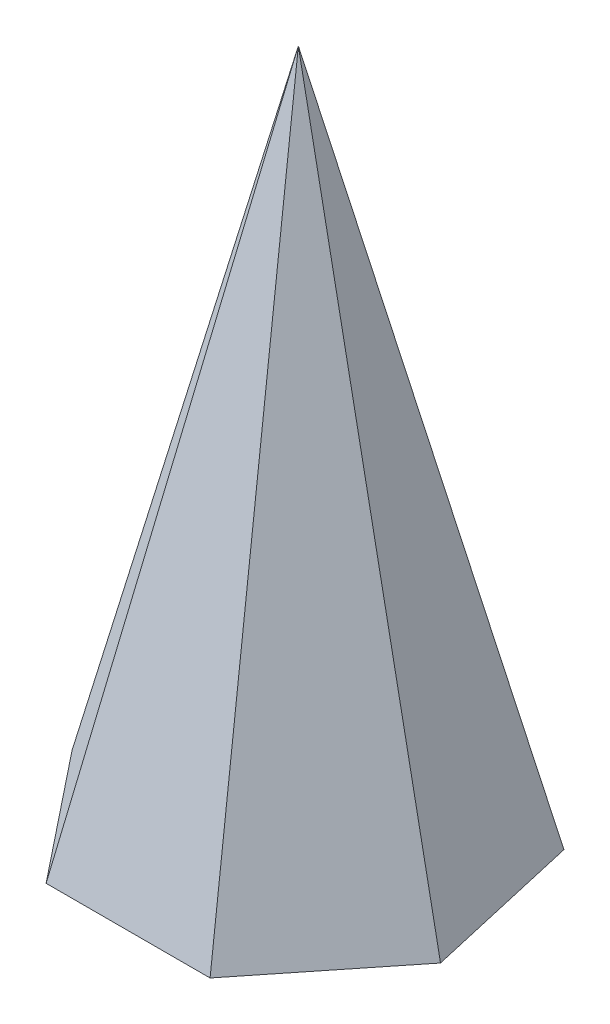
SolidWorks part; units mm, degrees
ref_plane "Front" through (0, 0, 0) normal (0, 0, 1) x (1, 0, 0)
ref_plane "Top" through (0, 0, 0) normal (0, 1, 0) x (1, 0, 0)
ref_plane "Right" through (0, 0, 0) normal (1, 0, 0) x (0, 0, -1)
sketch "Sketch1" plane through (0, 0, 0) normal (0, 1, 0) x (1, 0, 0)
  line L1 (5.4104, -1.2349) -> (4.3388, 3.4601)
  line L2 (4.3388, 3.4601) -> (0, 5.5496)
  line L3 (0, 5.5496) -> (-4.3388, 3.4601)
  line L4 (-4.3388, 3.4601) -> (-5.4104, -1.2349)
  line L5 (-5.4104, -1.2349) -> (-2.4079, -5)
  line L6 (-2.4079, -5) -> (2.4079, -5)
  line L7 (2.4079, -5) -> (5.4104, -1.2349)
  circle A0 centre (0, 0) radius 5 construction
  dimension "D1" = 10
sketch "Sketch2" plane through (0, 0, 0) normal (0, 0, 1) x (1, 0, 0)
  point P0 (0, 20)
  dimension "D1" = 20
loft "Loft1" add profiles "Sketch2", "Sketch1"
